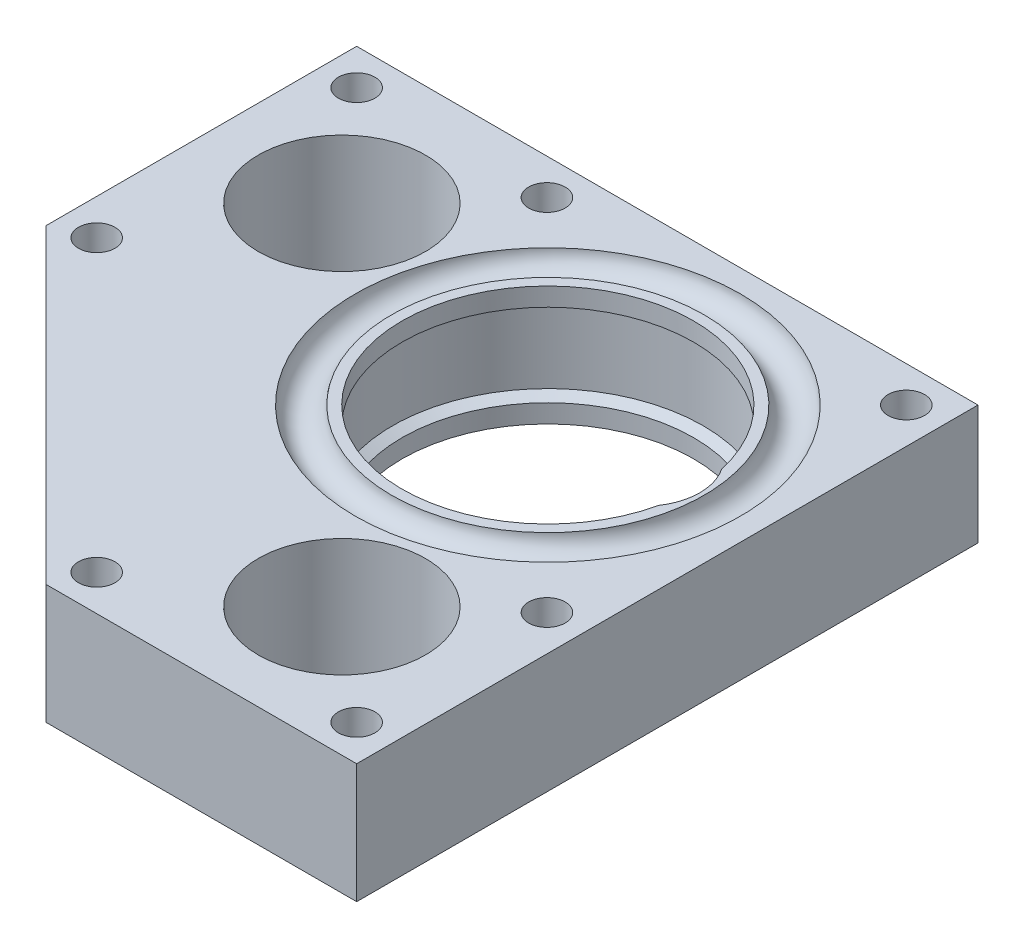
SolidWorks part; units mm, degrees
material "Markforged"
ref_plane "Front Plane" through (0, 0, 0) normal (0, 0, 1) x (1, 0, 0)
ref_plane "Top Plane" through (0, 0, 0) normal (0, 1, 0) x (1, 0, 0)
ref_plane "Right Plane" through (0, 0, 0) normal (1, 0, 0) x (0, 0, -1)
sketch "Sketch1" plane through (0, 0, 0) normal (1, 0, 0) x (0, 0, -1)
  line L0 (-20.6375, 0) -> (-26.9875, 0)
  line L1 (-26.9875, 0) -> (-26.9875, 7.9375)
  line L2 (-26.9875, 7.9375) -> (-25.5872, 7.9375)
  line L3 (0, 0) -> (0, 7.9375) construction
  line L4 (-19.3675, 7.9375) -> (-20.7678, 7.9375)
  line L5 (-19.8849, 8.0645) -> (-1.5141, 8.0645) construction
  line L6 (-19.3675, 7.9375) -> (-19.3675, 5.4957)
  line L7 (-19.3675, 5.4957) -> (-20.6375, 4.7625)
  line L8 (-20.6375, 4.7625) -> (-20.6375, 0)
  line L9 (0, 0) -> (-20.6375, 0) construction
  line L10 (0, 7.9375) -> (-19.3675, 7.9375) construction
  arc A0 (-20.7678, 7.9375) -> (-25.5872, 7.9375) centre (-23.1775, 8.0645) cw
  dimension "D4" = 2.413
  dimension "D1" = 7.9375
  dimension "D2" = 26.9875
  dimension "D3" = 23.1775
  dimension "D5" = 0.254
  dimension "D6" = 1.27
  dimension "D7" = 3.81
  dimension "D8" = 4.7625
  dimension "D9" = 30
revolve "Revolve1" add sketch "Sketch1" angle 360 about L3
mirror "Mirror1" about plane through (0, 0, 20.6375) normal (0, 1, 0) of bodies 101
sketch "Sketch3" plane through (0, 0, 0) normal (0, 1, 0) x (1, 0, 0)
  line L0 (0, 0) -> (12.7, 0) construction
  circle A0 centre (12.7, 0) radius 7.493
  dimension "D1" = 14.986
  dimension "D2" = 12.7
extrude "Cut-Extrude2" cut sketch "Sketch3" against normal through all both and the other way through all
sketch "Sketch4" plane through (0, 7.9375, 0) normal (0, 1, 0) x (1, 0, 0)
  line L0 (28.575, 1.6211) -> (28.575, 52.2844) construction
  line L1 (-16.5085, 28.575) -> (13.8355, 28.575) construction
  line L2 (28.575, 0) -> (0, 0) construction
  line L3 (0, 0) -> (0, 28.575) construction
  line L4 (-36.8902, 28.575) -> (-36.8902, 9.525) construction
  line L5 (-36.8902, 9.525) -> (0, 0) construction
  line L6 (0, 0) -> (9.525, -36.8902) construction
  line L7 (9.525, -36.8902) -> (28.575, -36.8902) construction
  line L8 (28.575, 28.575) -> (-53.975, 28.575)
  line L9 (-53.975, 28.575) -> (-53.975, -12.7)
  line L10 (-12.7, -53.975) -> (28.575, -53.975)
  line L11 (28.575, -53.975) -> (28.575, 28.575)
  line L12 (-53.975, -12.7) -> (-12.7, -53.975)
  line L13 (-53.975, -12.7) -> (-53.975, -53.975) construction
  line L14 (-53.975, -53.975) -> (-12.7, -53.975) construction
  circle A0 centre (-36.8902, 9.525) radius 11.1125
  circle A1 centre (9.525, -36.8902) radius 11.1125
  circle A4 centre (0, 0) radius 26.924
  dimension "D3" = 22.225
  dimension "D6" = 53.848
  dimension "D1" = 28.575
  dimension "D2" = 38.1
  dimension "D4" = 19.05
  dimension "D5" = 82.55
extrude "Boss-Extrude1" add sketch "Sketch4" against normal through all
sketch "Sketch7" plane through (0, 7.9375, 0) normal (0, 1, 0) x (1, 0, 0)
  line L5 (28.575, -53.975) -> (28.575, 28.575)
  line L6 (28.575, 28.575) -> (-53.975, 28.575)
  line L7 (-53.975, 28.575) -> (-53.975, -12.7)
  line L8 (-53.975, -12.7) -> (-12.7, -53.975)
  line L9 (-12.7, -53.975) -> (28.575, -53.975)
  line L10 (28.575, -53.975) -> (28.575, 28.575)
  line L11 (28.575, 28.575) -> (-53.975, 28.575)
  line L12 (-53.975, 28.575) -> (-53.975, -12.7)
  line L13 (-53.975, -12.7) -> (-12.7, -53.975)
  line L14 (-12.7, -53.975) -> (28.575, -53.975)
  circle A0 centre (0, 0) radius 6.35
  dimension "D2" = 12.7
  dimension "D1" = 0
extrude "Boss-Extrude2" add sketch "Sketch7" along normal blind 4.7625 from offset 22.225 separate body
sketch "Sketch5" plane through (0, 7.9375, 0) normal (0, 1, 0) x (1, 0, 0)
  line L0 (28.575, 28.575) -> (-53.975, 28.575) construction
  line L1 (28.575, -53.975) -> (28.575, 28.575) construction
  line L2 (23.8125, 23.8125) -> (-23.9339, 23.8125) construction
  line L3 (-23.9339, 23.8125) -> (-49.2125, 23.8125) construction
  line L4 (-53.975, 28.575) -> (-53.975, -12.7) construction
  line L5 (-29.4253, 17.7569) -> (-23.9339, 23.8125) construction
  line L6 (-23.9339, 23.8125) -> (-18.1388, 18.0468) construction
  line L7 (-53.975, -12.7) -> (-12.7, -53.975) construction
  line L8 (-33.3375, -33.3375) -> (28.575, 28.575) construction
  circle A0 centre (23.8125, 23.8125) radius 4.7625 construction
  circle A1 centre (23.8125, 23.8125) radius 2.4257
  circle A2 centre (-49.2125, 23.8125) radius 2.4257
  circle A3 centre (-49.2125, 23.8125) radius 4.7625 construction
  circle A4 centre (-23.9339, 23.8125) radius 2.4257
  circle A5 centre (-36.8902, 9.525) radius 11.1125 construction
  circle A6 centre (0, 0) radius 25.5872 construction
  circle A7 centre (-49.2125, -10.7273) radius 4.7625 construction
  circle A8 centre (-49.2125, -10.7273) radius 2.4257
  circle A9 centre (23.8125, -23.9339) radius 2.4257
  circle A10 centre (23.8125, -49.2125) radius 2.4257
  circle A11 centre (-10.7273, -49.2125) radius 2.4257
  point P23 (-36.8902, 9.525)
  dimension "D1" = 9.525
  dimension "D2" = 4.8514
extrude "Cut-Extrude3" cut sketch "Sketch5" against normal through all both and the other way through all
sketch "Sketch8" plane through (0, 7.9375, 0) normal (0, 1, 0) x (1, 0, 0)
  line L0 (-49.2125, 18.923) -> (-53.975, 18.923)
  line L1 (-53.975, 28.575) -> (-53.975, -12.7) construction
  line L2 (-53.975, 18.923) -> (-53.975, 28.575)
  line L3 (-53.975, 28.575) -> (-44.323, 28.575)
  line L4 (28.575, 28.575) -> (-53.975, 28.575) construction
  line L5 (-44.323, 28.575) -> (-44.323, 23.8125)
  line L6 (-28.8234, 23.8125) -> (-28.8234, 28.575)
  line L7 (-28.8234, 28.575) -> (-19.0444, 28.575)
  line L8 (-19.0444, 28.575) -> (-19.0444, 23.8125)
  line L9 (18.923, 23.8125) -> (18.923, 28.575)
  line L10 (18.923, 28.575) -> (28.575, 28.575)
  line L11 (28.575, 28.575) -> (28.575, 18.923)
  line L12 (28.575, -53.975) -> (28.575, 28.575) construction
  line L13 (28.575, 18.923) -> (23.8125, 18.923)
  line L14 (-49.2125, -5.8378) -> (-53.975, -5.8378)
  line L15 (-53.975, -5.8378) -> (-53.975, -12.7)
  line L16 (-53.975, -12.7) -> (-49.1227, -17.5523)
  line L17 (-53.975, -12.7) -> (-12.7, -53.975) construction
  line L18 (-49.1227, -17.5523) -> (-45.7551, -14.1847)
  line L19 (28.575, 28.575) -> (-33.3375, -33.3375) construction
  line L20 (28.575, -19.0444) -> (23.8125, -19.0444)
  line L21 (28.575, -28.8234) -> (28.575, -19.0444)
  line L22 (23.8125, -28.8234) -> (28.575, -28.8234)
  line L23 (28.575, -44.323) -> (23.8125, -44.323)
  line L24 (28.575, -53.975) -> (28.575, -44.323)
  line L25 (18.923, -53.975) -> (28.575, -53.975)
  line L26 (18.923, -49.2125) -> (18.923, -53.975)
  line L27 (-17.5523, -49.1227) -> (-14.1847, -45.7551)
  line L28 (-12.7, -53.975) -> (-17.5523, -49.1227)
  line L29 (-5.8378, -53.975) -> (-12.7, -53.975)
  line L30 (-5.8378, -49.2125) -> (-5.8378, -53.975)
  arc A0 (-49.2125, 18.923) -> (-44.323, 23.8125) centre (-49.2125, 23.8125) ccw
  arc A1 (-28.8234, 23.8125) -> (-19.0444, 23.8125) centre (-23.9339, 23.8125) ccw
  arc A2 (18.923, 23.8125) -> (23.8125, 18.923) centre (23.8125, 23.8125) ccw
  arc A6 (-45.7551, -14.1847) -> (-49.2125, -5.8378) centre (-49.2125, -10.7273) ccw
  arc A7 (-53.975, 24.9197) -> (-49.2125, 18.923) centre (-49.2125, 23.8125) ccw construction
  arc A8 (-48.1053, 28.575) -> (-53.975, 24.9197) centre (-49.2125, 23.8125) ccw construction
  arc A9 (-44.323, 23.8125) -> (-48.1053, 28.575) centre (-49.2125, 23.8125) ccw construction
  arc A10 (-22.8267, 28.575) -> (-28.8234, 23.8125) centre (-23.9339, 23.8125) ccw construction
  arc A11 (-19.0444, 23.8125) -> (-22.8267, 28.575) centre (-23.9339, 23.8125) ccw construction
  arc A12 (-51.7972, -14.8778) -> (-45.7551, -14.1847) centre (-49.2125, -10.7273) ccw construction
  arc A13 (-53.975, -11.8345) -> (-51.7972, -14.8778) centre (-49.2125, -10.7273) ccw construction
  arc A14 (-49.2125, -5.8378) -> (-53.975, -11.8345) centre (-49.2125, -10.7273) ccw construction
  arc A15 (23.8125, 18.923) -> (28.575, 22.7053) centre (23.8125, 23.8125) ccw construction
  arc A16 (28.575, 22.7053) -> (24.9197, 28.575) centre (23.8125, 23.8125) ccw construction
  arc A17 (24.9197, 28.575) -> (18.923, 23.8125) centre (23.8125, 23.8125) ccw construction
  arc A18 (23.8125, -19.0444) -> (28.575, -22.8267) centre (23.8125, -23.9339) cw construction
  arc A19 (28.575, -22.8267) -> (23.8125, -28.8234) centre (23.8125, -23.9339) cw construction
  arc A20 (23.8125, -28.8234) -> (23.8125, -19.0444) centre (23.8125, -23.9339) cw
  arc A21 (23.8125, -44.323) -> (28.575, -48.1053) centre (23.8125, -49.2125) cw construction
  arc A22 (28.575, -48.1053) -> (24.9197, -53.975) centre (23.8125, -49.2125) cw construction
  arc A23 (24.9197, -53.975) -> (18.923, -49.2125) centre (23.8125, -49.2125) cw construction
  arc A24 (18.923, -49.2125) -> (23.8125, -44.323) centre (23.8125, -49.2125) cw
  arc A25 (-5.8378, -49.2125) -> (-11.8345, -53.975) centre (-10.7273, -49.2125) cw construction
  arc A26 (-11.8345, -53.975) -> (-14.8778, -51.7972) centre (-10.7273, -49.2125) cw construction
  arc A27 (-14.8778, -51.7972) -> (-14.1847, -45.7551) centre (-10.7273, -49.2125) cw construction
  arc A28 (-14.1847, -45.7551) -> (-5.8378, -49.2125) centre (-10.7273, -49.2125) cw
  dimension "D1" = 9.779
extrude "Cut-Extrude4" [suppressed] cut sketch "Sketch8" against normal blind 3.175
delete or keep bodies "Body-Delete/Keep 1" [suppressed] type delete bodies bodies 106
delete or keep bodies "Body-Delete/Keep 2" type delete bodies bodies 108
